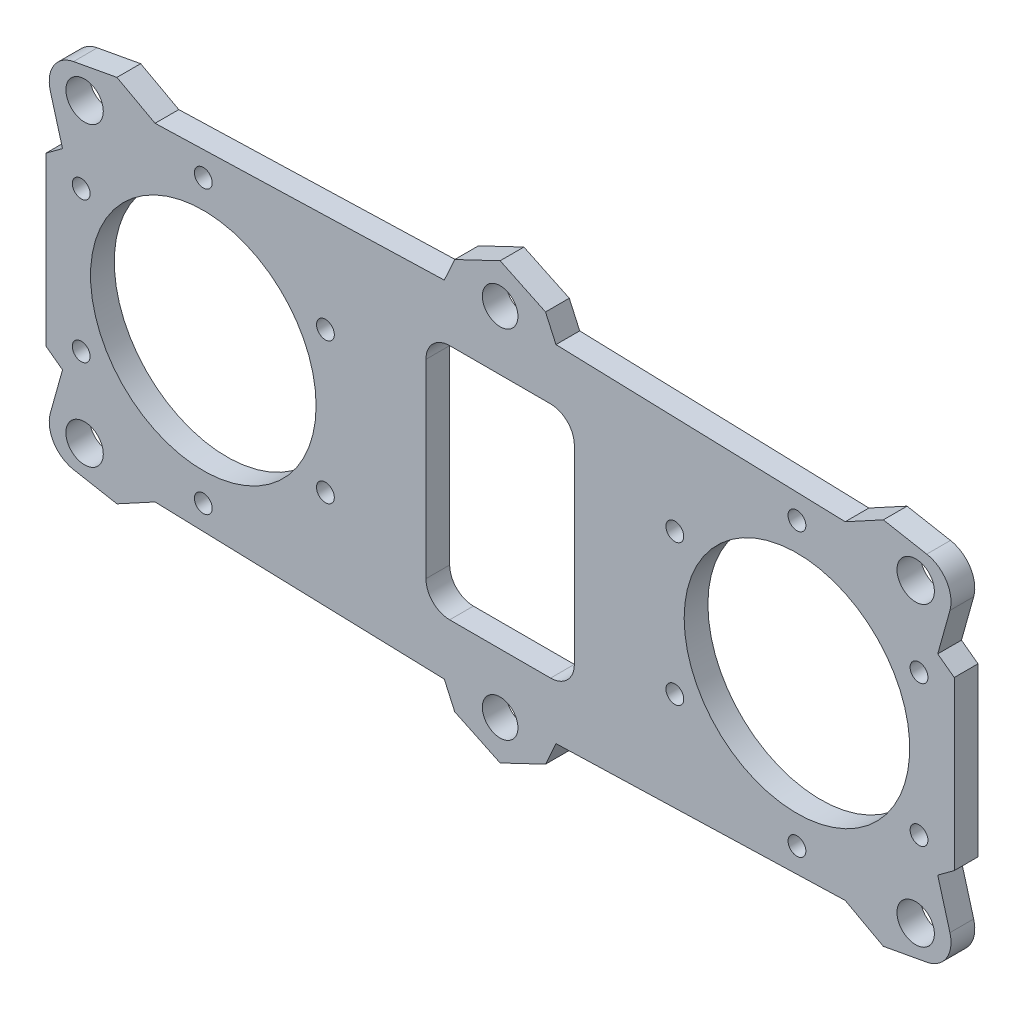
SolidWorks part; units mm, degrees
ref_plane "Front Plane" through (0, 0, 0) normal (0, 0, 1) x (1, 0, 0)
ref_plane "Top Plane" through (0, 0, 0) normal (0, 1, 0) x (1, 0, 0)
ref_plane "Right Plane" through (0, 0, 0) normal (1, 0, 0) x (0, 0, -1)
sketch "Sketch1" plane through (0, 0, 0) normal (0, 0, 1) x (1, 0, 0)
  line L0 (0, 36.6328) -> (-7.6473, 32.9908)
  line L1 (-7.6473, 32.9908) -> (-9.4053, 29.1042)
  line L2 (-9.4053, 29.1042) -> (-58.127, 27.6228)
  line L3 (-58.127, 27.6228) -> (-76.5, 14.0859)
  line L4 (-76.5, 14.0859) -> (-76.5, -14.0859)
  line L5 (-87.0431, 0) -> (20.0163, 0) construction
  line L6 (0, 32.2788) -> (0, 0) construction
  line L7 (76.5, 14.0859) -> (76.5, -14.0859)
  line L8 (58.127, 27.6228) -> (76.5, 14.0859)
  line L9 (9.4053, 29.1042) -> (58.127, 27.6228)
  line L10 (7.6473, 32.9908) -> (9.4053, 29.1042)
  line L11 (0, 36.6328) -> (7.6473, 32.9908)
  line L12 (0, -36.6328) -> (7.6473, -32.9908)
  line L13 (7.6473, -32.9908) -> (9.4053, -29.1042)
  line L14 (9.4053, -29.1042) -> (58.127, -27.6228)
  line L15 (58.127, -27.6228) -> (76.5, -14.0859)
  line L16 (-58.127, -27.6228) -> (-76.5, -14.0859)
  line L17 (-9.4053, -29.1042) -> (-58.127, -27.6228)
  line L18 (-7.6473, -32.9908) -> (-9.4053, -29.1042)
  line L19 (0, -36.6328) -> (-7.6473, -32.9908)
  circle A0 centre (0, 30) radius 3
  circle A1 centre (-50, 0) radius 19
  circle A2 centre (50, 0) radius 19
  circle A3 centre (0, -30) radius 3
  point P35 (76.5, 0)
  point P36 (-76.5, 0)
  dimension "D1" = 6
  dimension "D2" = 38
  dimension "D3" = 60
  dimension "D4" = 100
  dimension "D5" = 153
extrude "Boss-Extrude1" add sketch "Sketch1" along normal blind 4
sketch "Sketch2" plane through (0, 0, 4) normal (0, 0, 1) x (1, 0, 0)
  line L1 (8.5, 20) -> (-8.5, 20)
  line L2 (12.5, 16) -> (12.5, -16)
  line L3 (8.5, -20) -> (-8.5, -20)
  line L4 (-12.5, 16) -> (-12.5, -16)
  line L5 (12.5, 20) -> (-12.5, -20) construction
  line L6 (12.5, -20) -> (-12.5, 20) construction
  arc A1 (8.5, 20) -> (12.5, 16) centre (8.5, 16) cw
  arc A2 (12.5, -16) -> (8.5, -20) centre (8.5, -16) cw
  arc A3 (-8.5, -20) -> (-12.5, -16) centre (-8.5, -16) cw
  arc A4 (-8.5, 20) -> (-12.5, 16) centre (-8.5, 16) ccw
  point P0 (0, 0)
  dimension "D1" = 4
  dimension "D2" = 25
  dimension "D3" = 40
extrude "Cut-Extrude1" cut sketch "Sketch2" against normal through all
sketch "Sketch3" plane through (0, 0, 4) normal (0, 0, 1) x (1, 0, 0)
  line L0 (-58.127, 27.6228) -> (-64.5519, 31.11)
  line L1 (-58.127, 27.6228) -> (-76.5, 14.0859) construction
  line L2 (-64.5519, 31.11) -> (-77.2451, 28.7738)
  line L3 (-77.2451, 28.7738) -> (-73.717, 16.1363)
  line L4 (-73.717, 16.1363) -> (-58.127, 27.6228)
  line L5 (0, 0) -> (0, 46.5274) construction
  line L6 (73.717, 16.1363) -> (58.127, 27.6228)
  line L7 (77.2451, 28.7738) -> (73.717, 16.1363)
  line L8 (64.5519, 31.11) -> (77.2451, 28.7738)
  line L9 (58.127, 27.6228) -> (64.5519, 31.11)
  line L10 (0, 0) -> (-26.0239, 0) construction
  line L11 (58.127, -27.6228) -> (64.5519, -31.11)
  line L12 (64.5519, -31.11) -> (77.2451, -28.7738)
  line L13 (77.2451, -28.7738) -> (73.717, -16.1363)
  line L14 (73.717, -16.1363) -> (58.127, -27.6228)
  line L15 (-73.717, -16.1363) -> (-58.127, -27.6228)
  line L16 (-77.2451, -28.7738) -> (-73.717, -16.1363)
  line L17 (-64.5519, -31.11) -> (-77.2451, -28.7738)
  line L18 (-58.127, -27.6228) -> (-64.5519, -31.11)
  line L19 (-9.4053, 29.1042) -> (-58.127, 27.6228) construction
  circle A0 centre (-70, 25) radius 3.15
  circle A1 centre (70, 25) radius 3.15
  circle A2 centre (-70, -25) radius 3.15
  circle A3 centre (70, -25) radius 3.15
  dimension "D1" = 6.3
  dimension "D2" = 70
  dimension "D3" = 25
extrude "Boss-Extrude2" add sketch "Sketch3" against normal up to surface (4 mm away) up to face at (0, 0, 0)
fillet "Fillet1" radius 5 4 edges at (-77.2451, 28.7738, 2) (-77.2451, -28.7738, 2) (77.2451, -28.7738, 2) (77.2451, 28.7738, 2)
sketch "Sketch4" plane through (0, 0, 4) normal (0, 0, 1) x (1, 0, 0)
  line L0 (0, 48.5627) -> (0, -47.8194) construction
  circle A0 centre (-50, 0) radius 23.75 construction
  circle A1 centre (-50, 23.75) radius 1.5
  circle A2 centre (-70.5681, 11.875) radius 1.5
  circle A3 centre (-70.5681, -11.875) radius 1.5
  circle A4 centre (-50, -23.75) radius 1.5
  circle A5 centre (-29.4319, -11.875) radius 1.5
  circle A6 centre (-29.4319, 11.875) radius 1.5
  circle A7 centre (29.4319, 11.875) radius 1.5
  circle A8 centre (29.4319, -11.875) radius 1.5
  circle A9 centre (50, -23.75) radius 1.5
  circle A10 centre (70.5681, -11.875) radius 1.5
  circle A11 centre (70.5681, 11.875) radius 1.5
  circle A12 centre (50, 23.75) radius 1.5
  point P21 (-50, 0)
  point P31 (50, 0)
  dimension "D1" = 47.5
  dimension "D3" = 3
  dimension "D2" = 6
extrude "Cut-Extrude2" cut sketch "Sketch4" against normal through all
